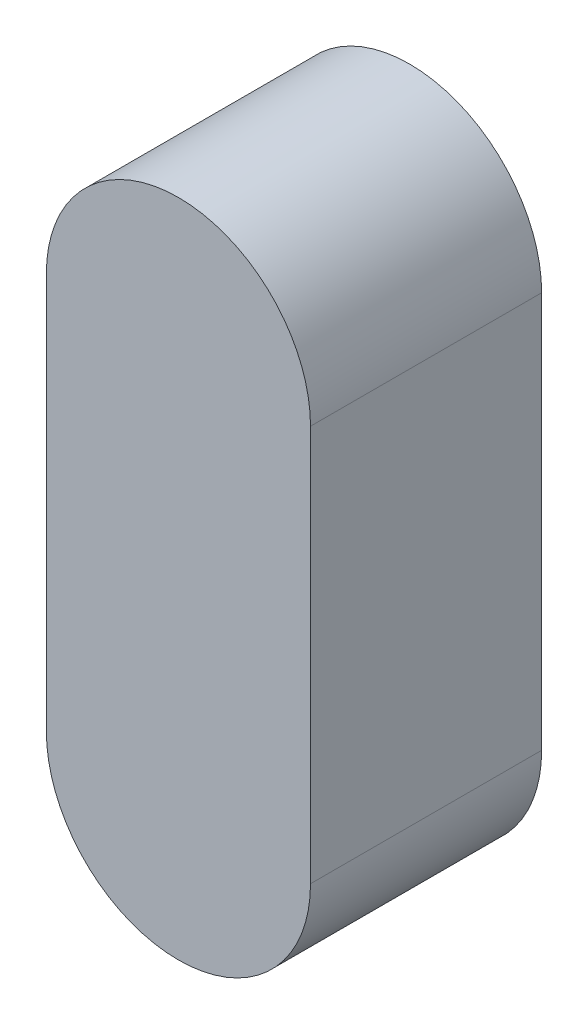
SolidWorks part; units mm, degrees
ref_plane "Přední rovina" through (0, 0, 0) normal (0, 0, 1) x (1, 0, 0)
ref_plane "Horní rovina" through (0, 0, 0) normal (0, 1, 0) x (1, 0, 0)
ref_plane "Pravá rovina" through (0, 0, 0) normal (1, 0, 0) x (0, 0, -1)
sketch "Skica1" plane through (0, 0, 0) normal (0, 0, 1) x (1, 0, 0)
  line L0 (0, 0) -> (0, 12) construction
  line L1 (-4, 0) -> (-4, 12)
  line L2 (4, 0) -> (4, 12)
  arc A0 (-4, 0) -> (4, 0) centre (0, 0) ccw
  arc A1 (4, 12) -> (-4, 12) centre (0, 12) ccw
  point P3 (0, 6)
  dimension "D2" = 20
  dimension "D1" = 8
extrude "Přidat vysunutím1" add sketch "Skica1" along normal blind 7
